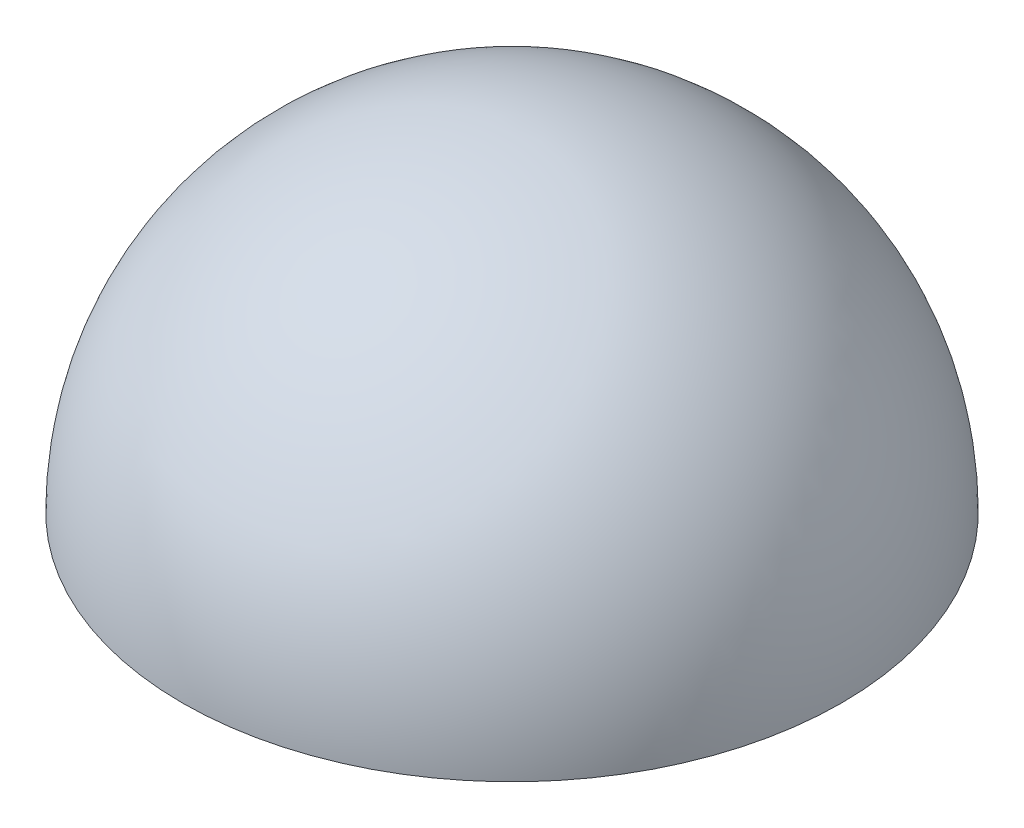
SolidWorks part; units mm, degrees
ref_plane "Front Plane" through (0, 0, 0) normal (0, 0, 1) x (1, 0, 0)
ref_plane "Top Plane" through (0, 0, 0) normal (0, 1, 0) x (1, 0, 0)
ref_plane "Right Plane" through (0, 0, 0) normal (1, 0, 0) x (0, 0, -1)
sketch "Sketch2" plane through (0, 0, 0) normal (0, 0, 1) x (1, 0, 0)
  line L1 (0, 76.75) -> (0, 84.25)
  line L2 (0, 0) -> (0, 109.8708) construction
  line L3 (0, 0) -> (-135.2835, 0) construction
  line L4 (-84.25, 0) -> (-76.75, 0)
  arc A0 (0, 84.25) -> (-84.25, 0) centre (0, 0) ccw
  arc A1 (0, 76.75) -> (-76.75, 0) centre (0, 0) ccw
  dimension "D1" = 168.5
  dimension "D2" = 153.5
revolve "Revolve1" add sketch "Sketch2" angle 360 about L2
